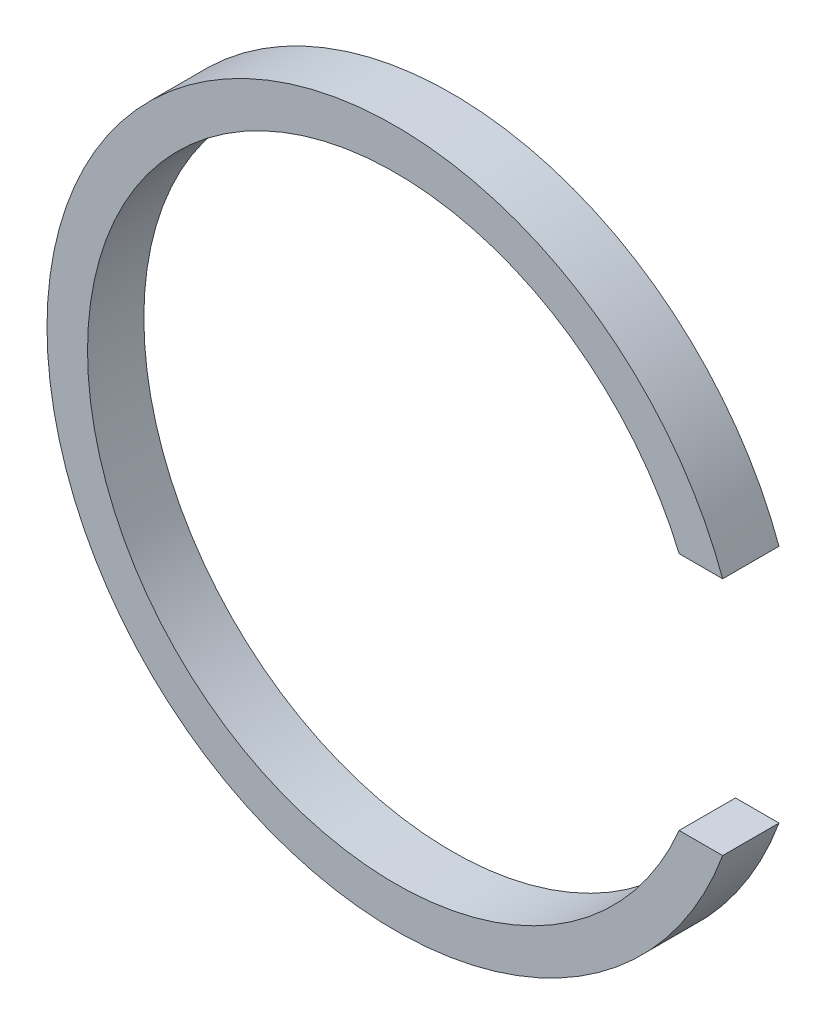
SolidWorks part; units mm, degrees
material "Silicon"
ref_plane "Front" through (0, 0, 0) normal (0, 0, 1) x (1, 0, 0)
ref_plane "Top" through (0, 0, 0) normal (0, 1, 0) x (1, 0, 0)
ref_plane "Right" through (0, 0, 0) normal (1, 0, 0) x (0, 0, -1)
sketch "Sketch1" plane through (0, 0, 0) normal (0, 0, 1) x (1, 0, 0)
  line L0 (70.0094, 29.575) -> (80.7547, 29.575)
  line L1 (70.0094, -29.5751) -> (80.7547, -29.5751)
  arc A0 (70.0094, 29.575) -> (70.0094, -29.5751) centre (0, 0) ccw
  arc A2 (80.7547, 29.575) -> (80.7547, -29.5751) centre (0, 0) ccw
  point P3 (0, 0)
  point P4 (0, 0)
  point P5 (0, 0)
  point P6 (0, 0)
  point P7 (0, 0)
  point P8 (0, 0)
  point P9 (0, 0)
  point P13 (0, 0)
  point P14 (0, 0)
extrude "Boss-Extrude1" add sketch "Sketch1" along normal blind 13.9 contours A0 L1 A2 L0
